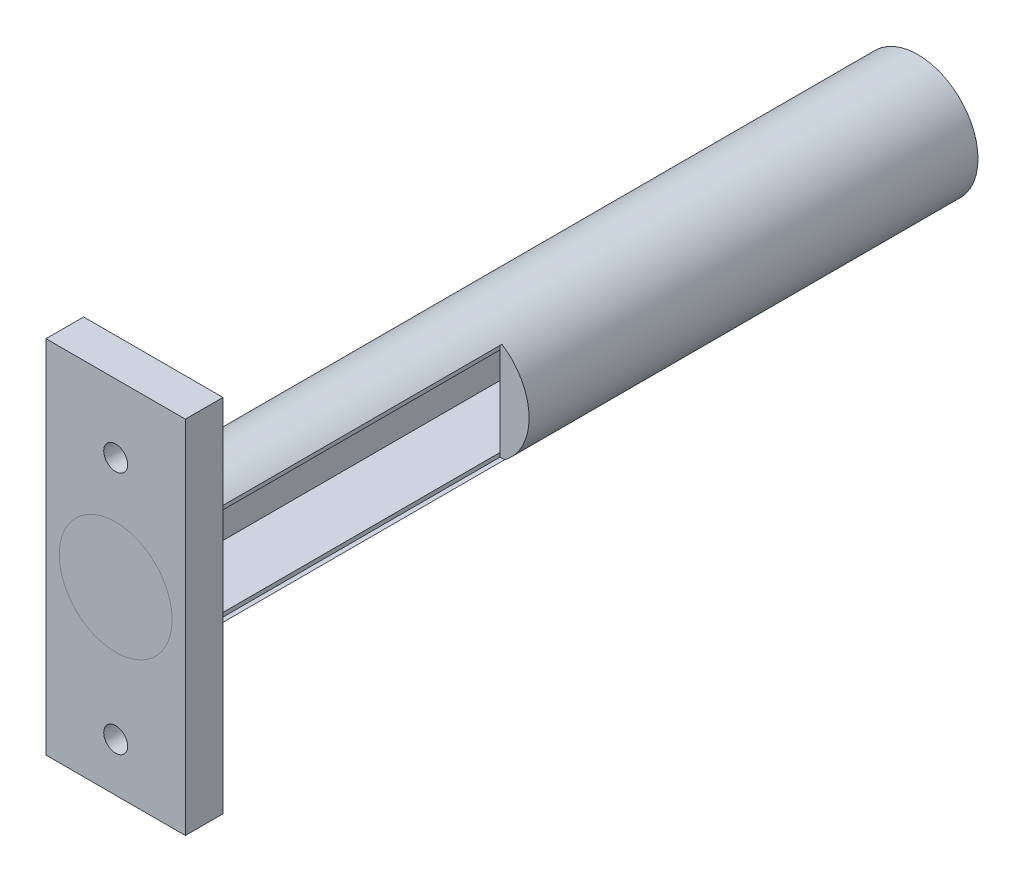
SolidWorks part; units mm, degrees
ref_plane "Front Plane" through (0, 0, 0) normal (0, 0, 1) x (1, 0, 0)
ref_plane "Top Plane" through (0, 0, 0) normal (0, 1, 0) x (1, 0, 0)
ref_plane "Right Plane" through (0, 0, 0) normal (1, 0, 0) x (0, 0, -1)
sketch "Sketch1" plane through (0, 0, 0) normal (0, 0, 1) x (1, 0, 0)
  circle A0 centre (0, 0) radius 8
  dimension "D1" = 16
extrude "Boss-Extrude1" add sketch "Sketch1" along normal blind 101.6
sketch "Sketch2" plane through (0, 0, 101.6) normal (0, 0, 1) x (1, 0, 0)
  line L1 (9.2598, -23.9637) -> (-9.2598, -23.9637)
  line L2 (9.2598, -23.9637) -> (9.2598, 23.9637)
  line L3 (9.2598, 23.9637) -> (-9.2598, 23.9637)
  line L4 (-9.2598, -23.9637) -> (-9.2598, 23.9637)
  line L5 (9.2598, -23.9637) -> (-9.2598, 23.9637) construction
  line L6 (9.2598, 23.9637) -> (-9.2598, -23.9637) construction
  point P0 (0, 0)
  point P6 (0, 0)
extrude "Boss-Extrude2" add sketch "Sketch2" along normal blind 5
sketch "Sketch3" plane through (0, 0, 106.6) normal (0, 0, 1) x (1, 0, 0)
  circle A0 centre (0, 0) radius 7.5
  dimension "D1" = 15
extrude "Boss-Extrude3" add sketch "Sketch3" along normal blind 0.0001
sketch "Sketch4" plane through (0, 0, 101.6) normal (0, 0, -1) x (-1, 0, 0)
  circle A0 centre (0, 14.8831) radius 1.59
  circle A1 centre (0, -17.5239) radius 1.59
  dimension "D1" = 3.18
  dimension "D2" = 3.18
extrude "Cut-Extrude1" cut sketch "Sketch4" against normal blind 34
sketch "Sketch7" plane through (0, 0, 0) normal (0, 0, -1) x (-1, 0, 0)
  circle A0 centre (0, 0) radius 3.185
  dimension "D1" = 6.37
extrude "Cut-Extrude2" cut sketch "Sketch7" against normal blind 4
sketch "Sketch8" plane through (0, 0, 4) normal (0, 0, -1) x (-1, 0, 0)
  line L1 (4.14, -5.9012) -> (-4.14, -5.9012)
  line L2 (4.14, -5.9012) -> (4.14, 5.9012)
  line L3 (4.14, 5.9012) -> (-4.14, 5.9012)
  line L4 (-4.14, -5.9012) -> (-4.14, 5.9012)
  line L5 (4.14, -5.9012) -> (-4.14, 5.9012) construction
  line L6 (4.14, 5.9012) -> (-4.14, -5.9012) construction
  point P0 (0, 0)
extrude "Cut-Extrude7" cut sketch "Sketch8" against normal blind 96
sketch "Sketch12" plane through (4.14, 0, 0) normal (-1, 0, 0) x (0, 0, 1)
  line L1 (100.3473, -6.4428) -> (59.657, -6.4428)
  line L2 (100.3473, -6.4428) -> (100.3473, 6.6804)
  line L3 (100.3473, 6.6804) -> (59.657, 6.6804)
  line L4 (59.657, -6.4428) -> (59.657, 6.6804)
  line L5 (100.3473, -6.4428) -> (59.657, 6.6804) construction
  line L6 (100.3473, 6.6804) -> (59.657, -6.4428) construction
  point P0 (80.0021, 0.1188)
extrude "Cut-Extrude8" cut sketch "Sketch12" against normal blind 35
sketch "Sketch13" plane through (-4.14, 0, 0) normal (1, 0, 0) x (0, 0, -1)
  line L1 (-95.8172, 5.4872) -> (-98.3734, 5.4872)
  line L2 (-95.8172, 5.4872) -> (-95.8172, -5.4872)
  line L3 (-95.8172, -5.4872) -> (-98.3734, -5.4872)
  line L4 (-98.3734, 5.4872) -> (-98.3734, -5.4872)
  line L5 (-95.8172, 5.4872) -> (-98.3734, -5.4872) construction
  line L6 (-95.8172, -5.4872) -> (-98.3734, 5.4872) construction
  point P0 (-97.0953, 0)
  point P5 (-92.908, 4.3829)
  point P6 (-93.3135, 5.2329)
  point P7 (-97.0953, 0)
extrude "Cut-Extrude9" cut sketch "Sketch13" against normal blind 35
